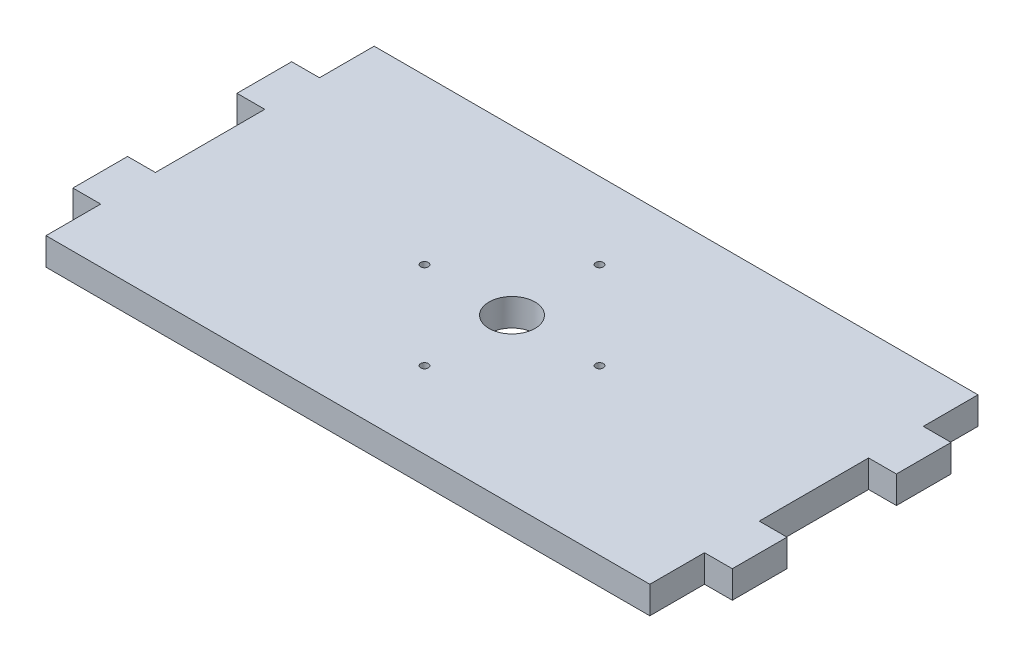
SolidWorks part; units mm, degrees
ref_plane "Front Plane" through (0, 0, 0) normal (0, 0, 1) x (1, 0, 0)
ref_plane "Top Plane" through (0, 0, 0) normal (0, 1, 0) x (1, 0, 0)
ref_plane "Right Plane" through (0, 0, 0) normal (1, 0, 0) x (0, 0, -1)
sketch "Sketch1" plane through (0, 0, 0) normal (0, 1, 0) x (1, 0, 0)
  line L1 (-35.052, -19.05) -> (35.052, -19.05)
  line L2 (-35.052, -19.05) -> (-35.052, 19.05)
  line L3 (-35.052, 19.05) -> (35.052, 19.05)
  line L4 (35.052, -19.05) -> (35.052, 19.05)
  line L5 (-35.052, -19.05) -> (35.052, 19.05) construction
  line L6 (-35.052, 19.05) -> (35.052, -19.05) construction
  point P0 (0, 0)
  dimension "D1" = 38.1
  dimension "D2" = 70.104
extrude "Boss-Extrude1" add sketch "Sketch1" along normal blind 3.175
sketch "Sketch2" plane through (0, 3.175, 0) normal (0, 1, 0) x (1, 0, 0)
  line L0 (35.052, 12.7) -> (35.052, 6.35)
  line L1 (35.052, 12.7) -> (38.2778, 12.7)
  line L2 (35.052, 6.35) -> (38.2778, 6.35)
  line L3 (38.2778, 12.7) -> (38.2778, 6.35)
  line L4 (35.052, -19.05) -> (35.052, 19.05) construction
  line L5 (35.052, -6.35) -> (35.052, -12.7)
  line L6 (35.052, -6.35) -> (38.2778, -6.35)
  line L7 (35.052, -12.7) -> (38.2778, -12.7)
  line L8 (38.2778, -6.35) -> (38.2778, -12.7)
  line L9 (35.052, 0) -> (38.2504, 0) construction
  dimension "D1" = 3.2258
  dimension "D2" = 3.2258
  dimension "D3" = 6.35
  dimension "D4" = 6.35
  dimension "D5" = 6.35
  dimension "D6" = 6.35
extrude "Boss-Extrude2" add sketch "Sketch2" against normal blind 3.175
mirror "Mirror1" about plane through (0, 0, 0) normal (1, 0, 0) of "Boss-Extrude2"
sketch "Sketch4" plane through (0, 3.175, 0) normal (0, 1, 0) x (1, 0, 0)
  line L0 (0, 0) -> (0, 10.16) construction
  circle A0 centre (0, 0) radius 2.667
  circle A1 centre (0, 10.16) radius 0.4445
  circle A2 centre (10.16, 0) radius 0.4445
  circle A3 centre (0, -10.16) radius 0.4445
  circle A4 centre (-10.16, 0) radius 0.4445
  dimension "D1" = 5.334
  dimension "D3" = 0.889
  dimension "D2" = 10.16
  dimension "D4" = 4
extrude "cut for servo horn mount holes" cut sketch "Sketch4" against normal through all
